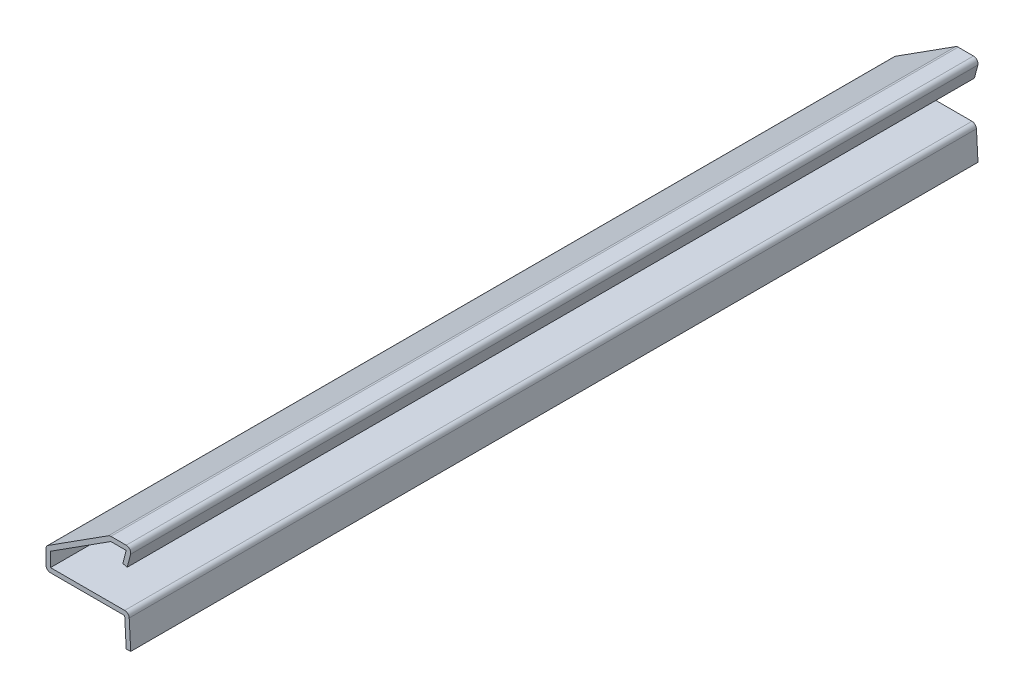
SolidWorks part; units mm, degrees
ref_plane "Front Plane" through (0, 0, 0) normal (0, 0, 1) x (1, 0, 0)
ref_plane "Top Plane" through (0, 0, 0) normal (0, 1, 0) x (1, 0, 0)
ref_plane "Right Plane" through (0, 0, 0) normal (1, 0, 0) x (0, 0, -1)
sketch "Sketch1" plane through (0, 0, 0) normal (0, 0, 1) x (1, 0, 0)
  line L0 (0, 0) -> (0, 26.0473) construction
  line L1 (-1.0145, -0.0551) -> (-1.3592, 6.2949)
  line L2 (-1.3592, 6.2949) -> (-19.05, 6.2949)
  line L3 (-19.05, 6.2949) -> (-19.05, 11.0574)
  line L4 (-19.05, 11.0574) -> (-4.7625, 20.1856)
  line L5 (-4.7625, 20.1856) -> (-1.016, 20.1856)
  line L6 (-0.0329, 18.9133) -> (-0.7937, 15.9946)
  line L7 (0, 0) -> (-0.3969, 7.3109)
  line L8 (-0.3969, 7.3109) -> (-18.034, 7.3109)
  line L9 (-18.034, 7.3109) -> (-18.034, 10.5009)
  line L10 (-18.034, 10.5009) -> (-4.4657, 19.1696)
  line L11 (-4.4657, 19.1696) -> (-1.016, 19.1696)
  line L12 (-1.016, 19.1696) -> (-1.7769, 16.2509)
  line L13 (-1.0145, -0.0551) -> (0, 0)
  line L14 (-0.7937, 15.9946) -> (-1.7769, 16.2509)
  line L15 (-4.7625, 20.1856) -> (0.2988, 20.1856) construction
  line L16 (0.2988, 20.1856) -> (-0.7937, 15.9946) construction
  arc A0 (-1.016, 20.1856) -> (-0.0329, 18.9133) centre (-1.016, 19.1696) cw
  point P1 (-1.3592, 20.1856)
  point P20 (0.2988, 20.1856)
  point P21 (0, 0)
  point P24 (-1.5697, 19.1696)
  point P25 (-0.0009, 19.2111)
  point P26 (0, 19.1696)
  dimension "D11" = 1.016
  dimension "D1" = 19.05
  dimension "D2" = 4.7625
  dimension "D3" = 9.1281
  dimension "D4" = 4.7625
  dimension "D5" = 6.35
  dimension "D6" = 13.8906
  dimension "D7" = 0.3969
  dimension "D8" = 0.7937
  dimension "D9" = 4.191
  dimension "D10" = 1.016
extrude "Boss-Extrude1" add sketch "Sketch1" against normal blind 190.5
fillet "Fillet1" radius 1.016 4 edges at (-19.05, 6.2949, -95.25) (-19.05, 11.0574, -95.25) (-4.7625, 20.1856, -95.25) (-0.3969, 7.3109, -95.25)
